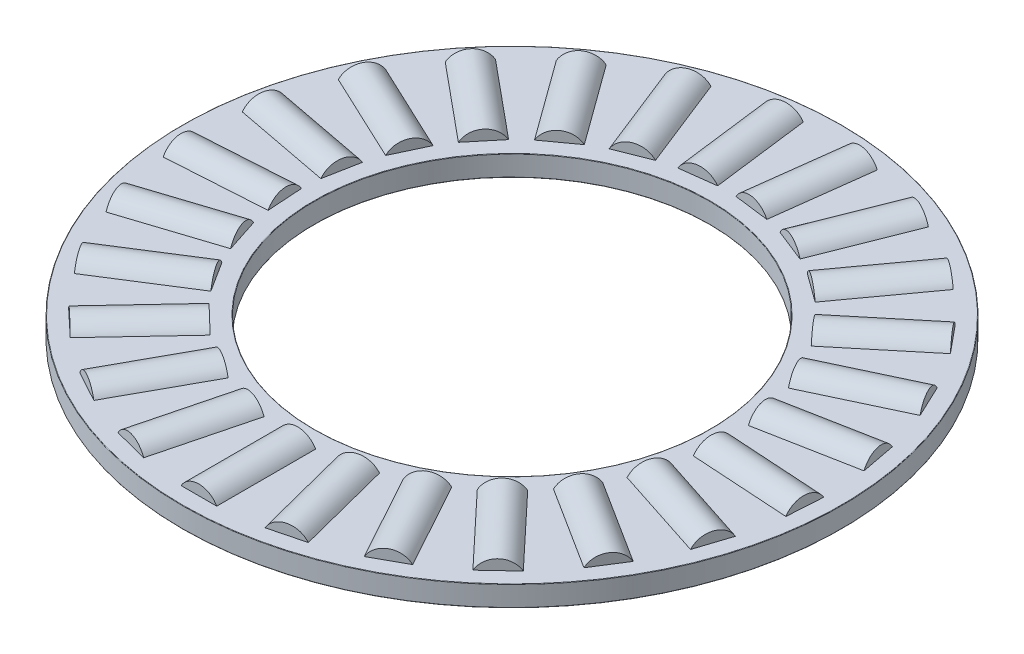
SolidWorks part; units mm, degrees
material "Cast Alloy Steel"
ref_plane "Front Plane" through (0, 0, 0) normal (0, 0, 1) x (1, 0, 0)
ref_plane "Top Plane" through (0, 0, 0) normal (0, 1, 0) x (1, 0, 0)
ref_plane "Right Plane" through (0, 0, 0) normal (1, 0, 0) x (0, 0, -1)
sketch "Sketch1" plane through (0, 0, 0) normal (1, 0, 0) x (0, 0, -1)
  line L0 (-15.875, 0) -> (15.875, 0) construction
  line L1 (0, -0.9922) -> (0, 0.9922) construction
  line L2 (-15.875, 0.4961) -> (-9.525, 0.4961)
  line L3 (-15.875, 0.4961) -> (-15.875, -0.4961)
  line L4 (-15.875, -0.4961) -> (-9.525, -0.4961)
  line L5 (-9.525, 0.4961) -> (-9.525, -0.4961)
  line L7 (-12.7, 0.9922) -> (-12.7, 0.4961) construction
  line L8 (-15.0813, 0.9922) -> (-10.3188, 0.9922) construction
  line L9 (-15.0813, 0.9922) -> (-15.0813, -0.9922) construction
  line L10 (-15.0813, -0.9922) -> (-10.3188, -0.9922) construction
  line L11 (-10.3188, 0.9922) -> (-10.3188, -0.9922) construction
  point P16 (-15.0813, 0)
  dimension "D1" = 4.7625
  dimension "OD" = 31.75
  dimension "Shaft Dia" = 19.05
  dimension "Th" = 1.9844
  dimension "D2" = 0.9922
  dimension "D3" = 6.35
revolve "Revolve1" add sketch "Sketch1" angle 360 about L1
sketch "Sketch3" plane through (0, 0, 0) normal (1, 0, 0) x (0, 0, -1)
  line L0 (-15.0813, 0.9922) -> (-15.0813, -0.9922) construction
  line L1 (-15.0813, 0) -> (-10.3188, 0)
  line L2 (-15.0813, 0) -> (-15.0813, 0.9922)
  line L3 (-15.0813, 0.9922) -> (-10.3188, 0.9922)
  line L4 (-10.3188, 0) -> (-10.3188, 0.9922)
revolve "Cut-Revolve1" cut sketch "Sketch3" angle 360 about L1
sketch "Sketch2" plane through (0, 0, 0) normal (1, 0, 0) x (0, 0, -1)
  line L1 (-15.0813, 0) -> (-10.3188, 0)
  line L2 (-15.0813, 0) -> (-15.0813, 0.9922)
  line L3 (-15.0813, 0.9922) -> (-10.3188, 0.9922)
  line L4 (-10.3188, 0) -> (-10.3188, 0.9922)
revolve "Revolve2" add sketch "Sketch2" angle 360 about L1
ref_axis "Axis1" through (0, 0.9922, 0) along (0, -1, 0)
pattern_circular "CirPattern1" count 25 every 14.4 about axis through (0, 0.9922, 0) along (0, -1, 0) of bodies 187 411
pattern_circular "CirPattern2" count 25 every 14.4 about axis through (0, 0, 0) along (0, 1, 0) of "Cut-Revolve1"
sketch "Sketch4" plane through (0, 0, 0) normal (1, 0, 0) x (0, 0, -1)
  line L0 (-15.875, 0.4961) -> (-15.875, -0.4961) construction
  line L1 (-15.875, 9.1091) -> (-9.525, 9.1091)
  line L2 (-15.875, 9.1091) -> (-15.875, 9.9219)
  line L3 (-15.875, 9.9219) -> (-9.525, 9.9219)
  line L4 (-9.525, 9.1091) -> (-9.525, 9.9219)
  line L5 (-15.875, -9.9219) -> (-9.525, -9.9219)
  line L6 (-15.875, -9.9219) -> (-15.875, -9.1091)
  line L7 (-15.875, -9.1091) -> (-9.525, -9.1091)
  line L8 (-9.525, -9.9219) -> (-9.525, -9.1091)
  line L10 (-9.525, 0.4961) -> (-9.525, -0.4961) construction
  line L11 (0, 0) -> (-15.875, 0) construction
  line L12 (-15.875, 0) -> (15.875, 0) construction
  line L13 (0, -0.9922) -> (0, 0.9922) construction
  dimension "Ht" = 19.8438
  dimension "Washer Th" = 0.8128
  dimension "Washer ID" = 19.05
  dimension "Washer OD" = 31.75
revolve "Revolve3" [suppressed] add sketch "Sketch4" angle 360 about L1
fillet "Fillet1" [suppressed] radius 0.0198
fillet "Fillet2" radius 0.0198 4 edges at (0, -0.4961, -9.525) (0, 0.4961, -9.525) (0, -0.4961, -15.875) (0, 0.4961, -15.875)
fillet "Fillet3" [suppressed] radius 0.0198
equation "\"D2@Sketch1\" = \"Th@Sketch1\"*.5"
equation "\"D1@Fillet1\" = \"Th@Sketch1\"*.01"
equation "\"D1@Fillet2\" = \"D1@Fillet1\""
equation "\"D1@Fillet3\" = \"D1@Fillet1\""
equation "\"D1@Sketch1\" = \"D3@Sketch1\"*.75"
equation "\"Angle@CirPattern1\" = 360/\"Rollers@CirPattern1\""
equation "\"Rollers@CirPattern1\" = \"OD@Sketch1\"*20"
equation "\"D1@CirPattern2\" = \"Rollers@CirPattern1\""
equation "\"D2@CirPattern2\" = \"Angle@CirPattern1\""
equation "\"Ht@Sketch4\" = \"Th@Sketch1\"*10"
